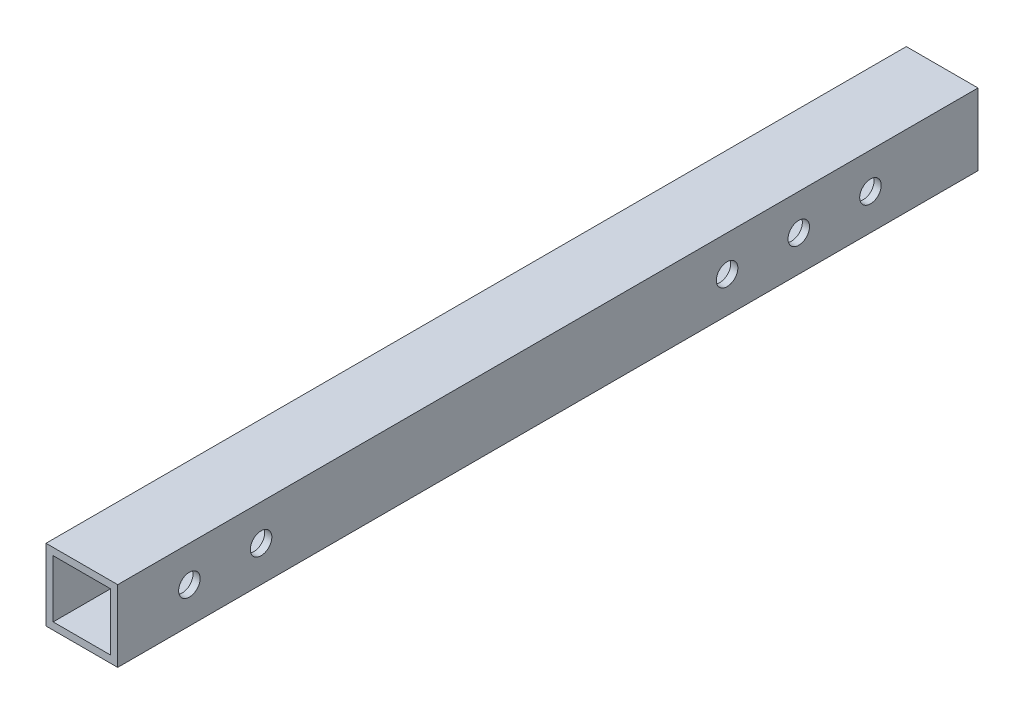
SolidWorks part; units mm, degrees
ref_plane "前视基准面" through (0, 0, 0) normal (0, 0, 1) x (1, 0, 0)
ref_plane "上视基准面" through (0, 0, 0) normal (0, 1, 0) x (1, 0, 0)
ref_plane "右视基准面" through (0, 0, 0) normal (1, 0, 0) x (0, 0, -1)
sketch "草图1" plane through (0, 0, 0) normal (1, 0, 0) x (0, 0, -1)
  line L1 (-46.6456, 10) -> (73.3544, 10)
  line L2 (-46.6456, 10) -> (-46.6456, 0)
  line L3 (-46.6456, 0) -> (73.3544, 0)
  line L4 (73.3544, 10) -> (73.3544, 0)
  circle A0 centre (-36.6456, 5) radius 1.5
  circle A1 centre (-26.6456, 5) radius 1.5
  circle A2 centre (58.3544, 5) radius 1.5
  circle A3 centre (48.3544, 5) radius 1.5
  circle A4 centre (38.3544, 5) radius 1.5
  dimension "D3" = 5
  dimension "D5" = 15
  dimension "D1" = 120
  dimension "D2" = 10
  dimension "D4" = 10
  dimension "D6" = 5
  dimension "D7" = 2
extrude "凸台-拉伸1" add sketch "草图1" along normal blind 10
sketch "草图2" plane through (0, 0, -73.3544) normal (0, 0, -1) x (-1, 0, 0)
  line L0 (-10, 0) -> (-10, 10) construction
  line L1 (-9, 9) -> (-1, 9)
  line L2 (-9, 9) -> (-9, 1)
  line L3 (-9, 1) -> (-1, 1)
  line L4 (-1, 9) -> (-1, 1)
  line L5 (-10, 10) -> (0, 10) construction
  dimension "D1" = 8
  dimension "D2" = 8
  dimension "D3" = 1
  dimension "D4" = 1
extrude "切除-拉伸1" cut sketch "草图2" against normal blind 120
